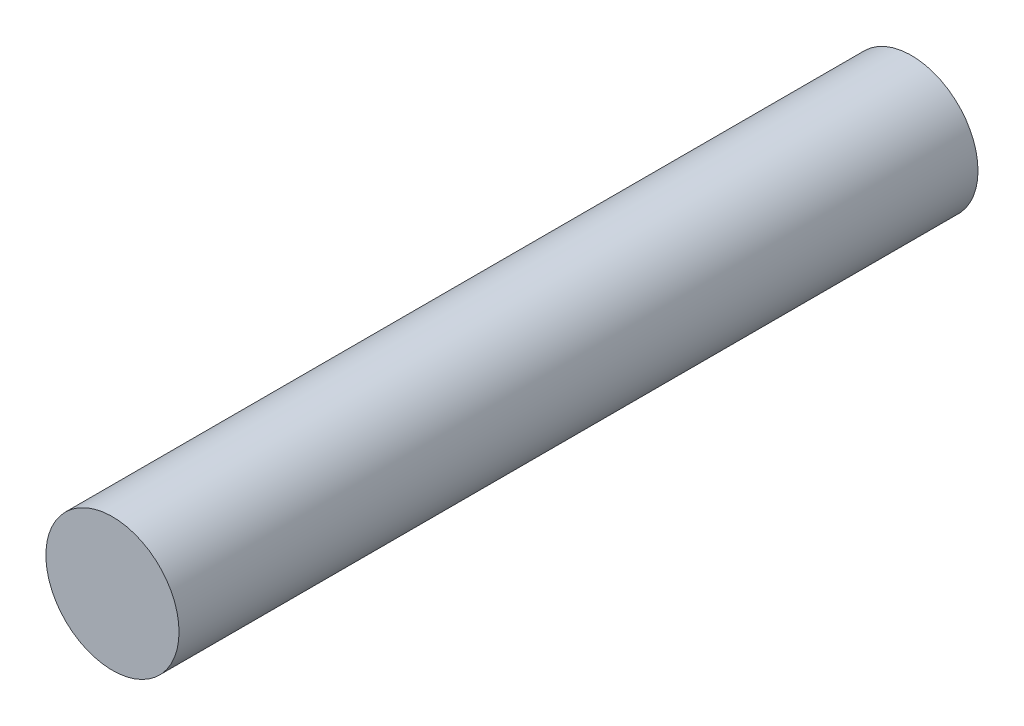
SolidWorks part; units mm, degrees
ref_plane "Front Plane" through (0, 0, 0) normal (0, 0, 1) x (1, 0, 0)
ref_plane "Top Plane" through (0, 0, 0) normal (0, 1, 0) x (1, 0, 0)
ref_plane "Right Plane" through (0, 0, 0) normal (1, 0, 0) x (0, 0, -1)
sketch "Sketch2" plane through (0, 0, 0) normal (0, 0, 1) x (1, 0, 0)
  circle A0 centre (0, 0) radius 10
  dimension "D1" = 20
extrude "Boss-Extrude1" add sketch "Sketch2" along normal blind 120
